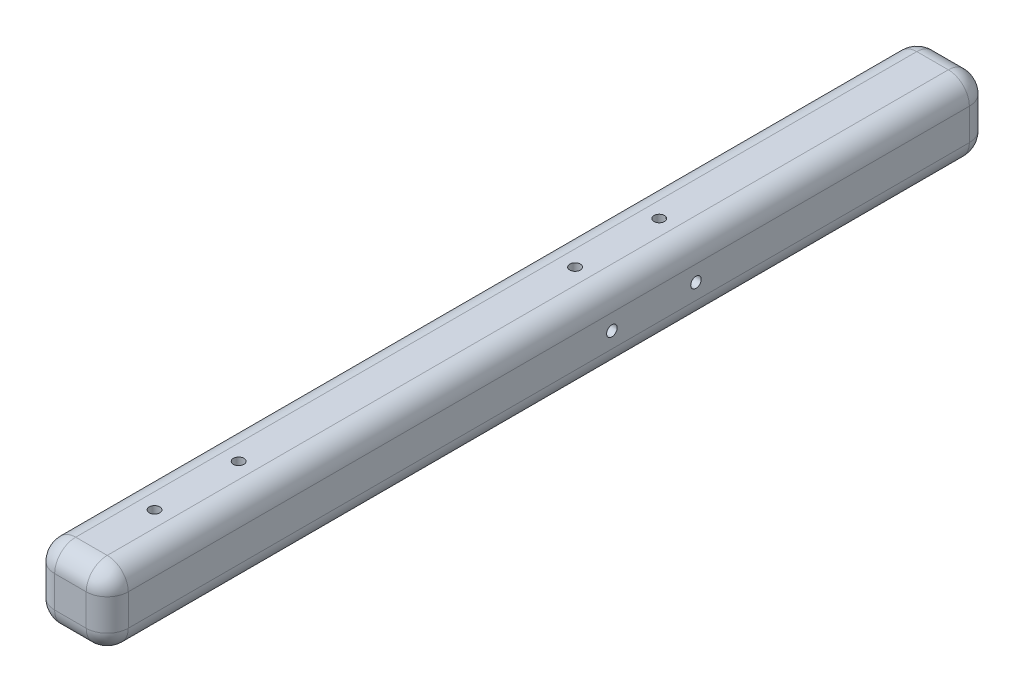
SolidWorks part; units mm, degrees
material "Pine"
ref_plane "Front Plane" through (0, 0, 0) normal (0, 0, 1) x (1, 0, 0)
ref_plane "Top Plane" through (0, 0, 0) normal (0, 1, 0) x (1, 0, 0)
ref_plane "Right Plane" through (0, 0, 0) normal (1, 0, 0) x (0, 0, -1)
sketch "Sketch1" plane through (0, 0, 0) normal (0, 0, 1) x (1, 0, 0)
  line L1 (-9.525, -22.225) -> (9.525, -22.225)
  line L2 (-22.225, -9.525) -> (-22.225, 9.525)
  line L3 (-9.525, 22.225) -> (9.525, 22.225)
  line L4 (22.225, -9.525) -> (22.225, 9.525)
  line L5 (-22.225, -22.225) -> (22.225, 22.225) construction
  line L6 (-22.225, 22.225) -> (22.225, -22.225) construction
  arc A0 (-9.525, -22.225) -> (-22.225, -9.525) centre (-9.525, -9.525) cw
  arc A1 (22.225, -9.525) -> (9.525, -22.225) centre (9.525, -9.525) cw
  arc A2 (22.225, 9.525) -> (9.525, 22.225) centre (9.525, 9.525) ccw
  arc A3 (-9.525, 22.225) -> (-22.225, 9.525) centre (-9.525, 9.525) ccw
  point P0 (0, 0)
  dimension "D3" = 12.7
  dimension "D1" = 44.45
  dimension "D2" = 44.45
extrude "Boss-Extrude1" add sketch "Sketch1" along normal blind 254
fillet "Fillet1" radius 12.7 8 edges at (18.5053, 18.5053, 0) (22.225, 0, 0) (18.5053, -18.5053, 0) (0, -22.225, 0) (-18.5053, -18.5053, 0) (-22.225, 0, 0) (-18.5053, 18.5053, 0) (0, 22.225, 0)
sketch "Sketch2" plane through (0, 22.225, 0) normal (0, 1, 0) x (1, 0, 0)
  line L0 (0, -1210.9207) -> (0, 48789.0793) construction
  line L2 (-1047.1464, -228.6) -> (48952.8536, -228.6) construction
  line L3 (-1039.9802, -177.8) -> (48960.0198, -177.8) construction
  line L4 (9.525, -254) -> (-9.525, -254) construction
  circle A0 centre (0, -177.8) radius 3.175
  circle A1 centre (0, -228.6) radius 3.175
  dimension "D3" = 6.35
  dimension "D4" = 6.35
  dimension "D1" = 25.4
  dimension "D2" = 50.8
extrude "Cut-Extrude1" cut sketch "Sketch2" against normal blind 12.7
sketch "Sketch3" plane through (0, 0, 0) normal (0, 1, 0) x (1, 0, 0)
  line L0 (0, -1052.1314) -> (0, 48947.8686) construction
pattern_circular "CirPattern2" count 2 every 90 about axis through (0, 0, 1052.1314) along (0, 0, -1) of "Cut-Extrude1"
sketch "Sketch4" plane through (0, 0, 254) normal (0, 0, 1) x (1, 0, 0)
  line L1 (-9.525, -22.225) -> (9.525, -22.225)
  line L2 (-22.225, -9.525) -> (-22.225, 9.525)
  line L3 (-9.525, 22.225) -> (9.525, 22.225)
  line L4 (22.225, -9.525) -> (22.225, 9.525)
  line L5 (-22.225, -22.225) -> (22.225, 22.225) construction
  line L6 (-22.225, 22.225) -> (22.225, -22.225) construction
  arc A0 (-9.525, -22.225) -> (-22.225, -9.525) centre (-9.525, -9.525) cw
  arc A1 (22.225, -9.525) -> (9.525, -22.225) centre (9.525, -9.525) cw
  arc A2 (22.225, 9.525) -> (9.525, 22.225) centre (9.525, 9.525) ccw
  arc A3 (-9.525, 22.225) -> (-22.225, 9.525) centre (-9.525, 9.525) ccw
  point P0 (0, 0)
  dimension "D3" = 12.7
  dimension "D1" = 44.45
  dimension "D2" = 44.45
extrude "Boss-Extrude2" add sketch "Sketch4" along normal blind 279.4
fillet "Fillet2" radius 12.7 8 edges at (18.5053, -18.5053, 533.4) (0, -22.225, 533.4) (-18.5053, -18.5053, 533.4) (-22.225, 0, 533.4) (-18.5053, 18.5053, 533.4) (0, 22.225, 533.4) (18.5053, 18.5053, 533.4) (22.225, 0, 533.4)
sketch "Sketch6" plane through (0, 22.225, 0) normal (0, 1, 0) x (1, 0, 0)
  line L0 (0, -1331.9027) -> (0, 48668.0973) construction
  line L2 (-1193.8308, -482.6) -> (48806.1692, -482.6) construction
  line L3 (-1190.8354, -431.8) -> (48809.1646, -431.8) construction
  line L4 (9.525, -533.4) -> (-9.525, -533.4) construction
  circle A0 centre (0, -431.8) radius 3.175
  circle A1 centre (0, -482.6) radius 3.175
  dimension "D3" = 6.35
  dimension "D4" = 6.35
  dimension "D1" = 50.8
  dimension "D2" = 50.8
extrude "Cut-Extrude3" cut sketch "Sketch6" against normal blind 12.7
